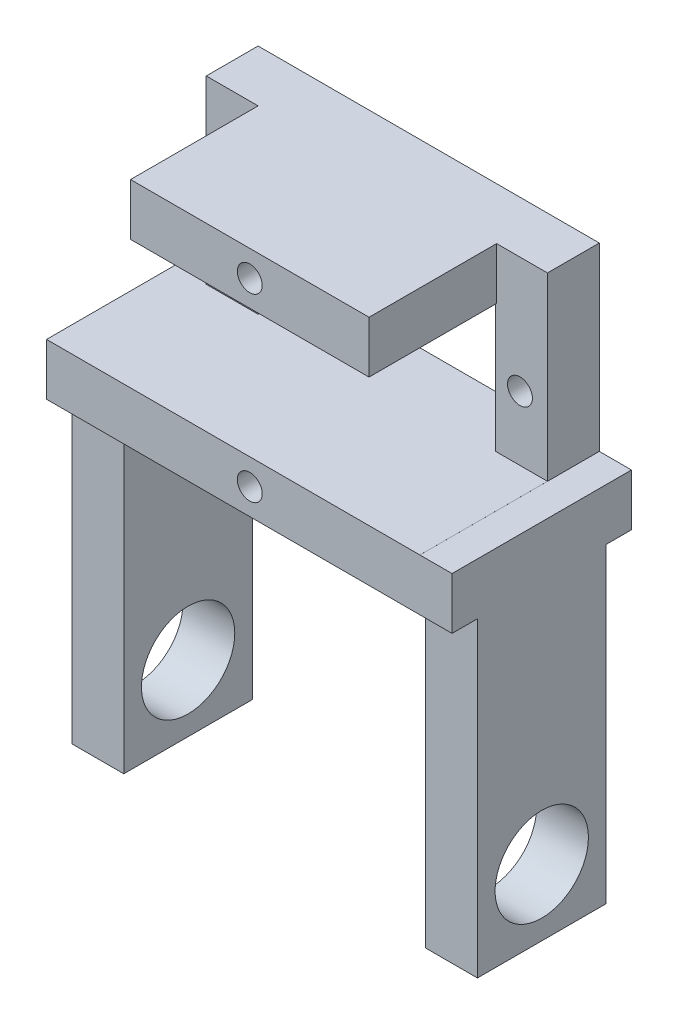
SolidWorks part; units mm, degrees
ref_plane "Front Plane" through (0, 0, 0) normal (0, 0, 1) x (1, 0, 0)
ref_plane "Top Plane" through (0, 0, 0) normal (0, 1, 0) x (1, 0, 0)
ref_plane "Right Plane" through (0, 0, 0) normal (1, 0, 0) x (0, 0, -1)
sketch "Sketch1" plane through (0, 0, 0) normal (0, 0, 1) x (1, 0, 0)
  line L1 (-16.45, 11.2) -> (16.45, 11.2)
  line L2 (-16.45, 11.2) -> (-16.45, -11.2)
  line L3 (-16.45, -11.2) -> (16.45, -11.2)
  line L4 (16.45, 11.2) -> (16.45, -11.2)
  line L5 (-16.45, 11.2) -> (16.45, -11.2) construction
  line L6 (-16.45, -11.2) -> (16.45, 11.2) construction
  point P0 (0, 0)
  dimension "D1" = 32.9
  dimension "22.4" = 22.4
extrude "Boss-Extrude1" add sketch "Sketch1" along normal blind 5
sketch "Sketch2" plane through (0, 0, 5) normal (0, 0, 1) x (1, 0, 0)
  line L0 (0, 0) -> (13.8, 0) construction
  line L1 (-11.45, 6.2) -> (11.45, 6.2)
  line L2 (-11.45, 6.2) -> (-11.45, -6.2)
  line L3 (-11.45, -6.2) -> (11.45, -6.2)
  line L4 (11.45, 6.2) -> (11.45, -6.2)
  line L5 (-11.45, 6.2) -> (11.45, -6.2) construction
  line L6 (-11.45, -6.2) -> (11.45, 6.2) construction
  line L7 (0, 0) -> (-13.8, 0) construction
  circle A0 centre (13.8, 0) radius 1.2
  circle A1 centre (-13.8, 0) radius 1.2
  point P0 (0, 0)
  dimension "D3" = 13.8
  dimension "D1" = 22.9
  dimension "D2" = 13.8
  dimension "12.4" = 12.4
extrude "Cut-Extrude2" cut sketch "Sketch2" against normal blind 5
sketch "Sketch3" plane through (0, 0, 5) normal (0, 0, 1) x (1, 0, 0)
  line L0 (16.45, 11.2) -> (-16.45, 11.2) construction
  line L1 (-11.45, 6.2) -> (11.5469, 6.2)
  line L2 (-11.45, 6.2) -> (-11.45, 11.2)
  line L3 (-11.45, 11.2) -> (11.5469, 11.2)
  line L4 (11.5469, 6.2) -> (11.5469, 11.2)
  line L5 (-16.45, -11.2) -> (16.45, -11.2) construction
  line L6 (-11.45, -6.2) -> (11.5469, -6.2)
  line L7 (-11.45, -6.2) -> (-11.45, -11.2)
  line L8 (-11.45, -11.2) -> (11.5469, -11.2)
  line L9 (11.5469, -6.2) -> (11.5469, -11.2)
extrude "Boss-Extrude2" add sketch "Sketch3" along normal blind 12.3
sketch "Sketch4" plane through (0, 0, 17.3) normal (0, 0, 1) x (1, 0, 0)
  line L0 (0.0484, 11.2) -> (0.0484, 6.2) construction
  line L1 (11.5469, 11.2) -> (-11.45, 11.2) construction
  line L2 (-11.45, 6.2) -> (11.5469, 6.2) construction
  line L3 (0.0484, -6.2) -> (0.0484, -11.2) construction
  line L4 (11.5469, -6.2) -> (-11.45, -6.2) construction
  line L5 (-11.45, -11.2) -> (11.5469, -11.2) construction
  circle A0 centre (0.0484, 8.7) radius 1.2
  circle A1 centre (0.0484, -8.7) radius 1.2
extrude "Cut-Extrude3" cut sketch "Sketch4" against normal blind 5
sketch "Sketch6" plane through (0, 0, 5) normal (0, 0, 1) x (1, 0, 0)
  line L0 (-11.45, 6.2) -> (-11.45, -6.2) construction
  line L1 (-16.45, -11.2) -> (-11.45, -11.2)
  line L2 (-16.45, -11.2) -> (-16.45, -6.2)
  line L3 (-16.45, -6.2) -> (-11.45, -6.2)
  line L4 (-11.45, -11.2) -> (-11.45, -6.2)
  line L5 (-11.45, -6.2) -> (-11.45, -11.2) construction
  line L6 (16.45, -11.2) -> (16.45, 11.2) construction
  line L7 (11.5469, -11.2) -> (16.45, -11.2)
  line L8 (11.5469, -11.2) -> (11.5469, -6.2)
  line L9 (11.5469, -6.2) -> (16.45, -6.2)
  line L10 (16.45, -11.2) -> (16.45, -6.2)
extrude "Boss-Extrude3" add sketch "Sketch6" along normal blind 12.3
sketch "Sketch8" plane through (16.45, 0, 0) normal (1, 0, 0) x (0, 0, -1)
  line L0 (0, -11.2) -> (0, 11.2) construction
  line L1 (-17.3, -11.2) -> (0, -11.2)
  line L2 (-17.3, -11.2) -> (-17.3, -6.2018)
  line L3 (-17.3, -6.2018) -> (0, -6.2018)
  line L4 (0, -11.2) -> (0, -6.2018)
extrude "Boss-Extrude4" add sketch "Sketch8" along normal blind 3.1
sketch "Sketch9" plane through (-16.45, 0, 0) normal (-1, 0, 0) x (0, 0, 1)
  line L1 (0, -11.2) -> (17.3, -11.2)
  line L2 (0, -11.2) -> (0, -6.2)
  line L3 (0, -6.2) -> (17.3, -6.2)
  line L4 (17.3, -11.2) -> (17.3, -6.2)
extrude "Boss-Extrude5" add sketch "Sketch9" along normal blind 3.1
sketch "Sketch10" plane through (0, -11.2, 0) normal (0, -1, 0) x (1, 0, 0)
  line L0 (19.55, 8.65) -> (17.05, 8.65) construction
  line L1 (19.55, 17.3) -> (19.55, 0) construction
  line L2 (-19.55, 8.65) -> (-17.05, 8.65) construction
  line L3 (-19.55, 0) -> (-19.55, 17.3) construction
  line L5 (14.55, 14.85) -> (19.55, 14.85)
  line L6 (14.55, 14.85) -> (14.55, 2.45)
  line L7 (14.55, 2.45) -> (19.55, 2.45)
  line L8 (19.55, 14.85) -> (19.55, 2.45)
  line L9 (14.55, 14.85) -> (19.55, 2.45) construction
  line L10 (14.55, 2.45) -> (19.55, 14.85) construction
  line L11 (-14.55, 14.85) -> (-19.55, 14.85)
  line L12 (-14.55, 14.85) -> (-14.55, 2.45)
  line L13 (-14.55, 2.45) -> (-19.55, 2.45)
  line L14 (-19.55, 14.85) -> (-19.55, 2.45)
  line L15 (-14.55, 14.85) -> (-19.55, 2.45) construction
  line L16 (-14.55, 2.45) -> (-19.55, 14.85) construction
  dimension "D1" = 12.4
sketch "Sketch18" plane through (0, -11.2, 0) normal (0, -1, 0) x (1, 0, 0)
  line L0 (-19.55, 8.65) -> (-17.05, 8.65) construction
  line L1 (-19.55, 0) -> (-19.55, 17.3) construction
  line L2 (19.55, 8.65) -> (17.05, 8.65) construction
  line L4 (19.55, 17.3) -> (19.55, 0) construction
  line L5 (-14.55, 2.45) -> (-19.55, 2.45)
  line L6 (-14.55, 2.45) -> (-14.55, 14.85)
  line L7 (-14.55, 14.85) -> (-19.55, 14.85)
  line L8 (-19.55, 2.45) -> (-19.55, 14.85)
  line L9 (-14.55, 2.45) -> (-19.55, 14.85) construction
  line L10 (-14.55, 14.85) -> (-19.55, 2.45) construction
  line L12 (14.55, 2.45) -> (19.55, 2.45)
  line L13 (14.55, 2.45) -> (14.55, 14.85)
  line L14 (14.55, 14.85) -> (19.55, 14.85)
  line L15 (19.55, 2.45) -> (19.55, 14.85)
  line L16 (14.55, 2.45) -> (19.55, 14.85) construction
  line L17 (14.55, 14.85) -> (19.55, 2.45) construction
  dimension "D1" = 12.4
extrude "Boss-Extrude7" add sketch "Sketch18" along normal blind 30
sketch "Sketch19" plane through (-19.55, 0, 0) normal (-1, 0, 0) x (0, 0, 1)
  line L0 (8.65, -41.2) -> (8.65, -34.8) construction
  line L1 (14.85, -41.2) -> (2.45, -41.2) construction
  circle A0 centre (8.65, -34.8) radius 4.5
extrude "Cut-Extrude6" cut sketch "Sketch19" against normal blind 30
sketch "Sketch20" plane through (19.55, 0, 0) normal (1, 0, 0) x (0, 0, -1)
  line L0 (-8.65, -41.2) -> (-8.65, -34.8) construction
  line L1 (-2.45, -41.2) -> (-14.85, -41.2) construction
  circle A0 centre (-8.65, -34.8) radius 4.5
extrude "Cut-Extrude7" cut sketch "Sketch20" against normal blind 30
extrude "Boss-Extrude6" add sketch "Sketch10" along normal blind 30
sketch "Sketch12" plane through (-19.55, 0, 0) normal (-1, 0, 0) x (0, 0, 1)
sketch "Sketch21" plane through (19.55, 0, 0) normal (1, 0, 0) x (0, 0, -1)
  line L0 (-8.65, -41.2) -> (-8.65, -34.8) construction
  line L1 (-2.45, -41.2) -> (-14.85, -41.2) construction
  circle A0 centre (-8.65, -34.8) radius 4.5
extrude "Cut-Extrude8" cut sketch "Sketch21" against normal blind 10
sketch "Sketch22" plane through (-14.55, 0, 0) normal (1, 0, 0) x (0, 0, -1)
  line L0 (-8.65, -41.2) -> (-8.65, -34.8) construction
  line L1 (-2.45, -41.2) -> (-14.85, -41.2) construction
  circle A0 centre (-8.65, -34.8) radius 4.5
extrude "Cut-Extrude9" cut sketch "Sketch22" against normal blind 10
sketch "Sketch23" plane through (-19.55, 0, 0) normal (-1, 0, 0) x (0, 0, 1)
  line L0 (8.65, -39.3) -> (8.65, -22.3) construction
  line L1 (5.65, -22.3) -> (4.6742, -32.6921)
  line L3 (12.6258, -32.6921) -> (11.65, -22.3)
  circle A0 centre (8.65, -34.8) radius 4.5 construction
  arc A1 (11.65, -22.3) -> (5.65, -22.3) centre (8.65, -22.3) ccw
  arc A2 (4.6742, -32.6921) -> (12.6258, -32.6921) centre (8.65, -34.8) cw
  dimension "D1" = 17
extrude "Cut-Extrude10" cut sketch "Sketch23" against normal blind 3
